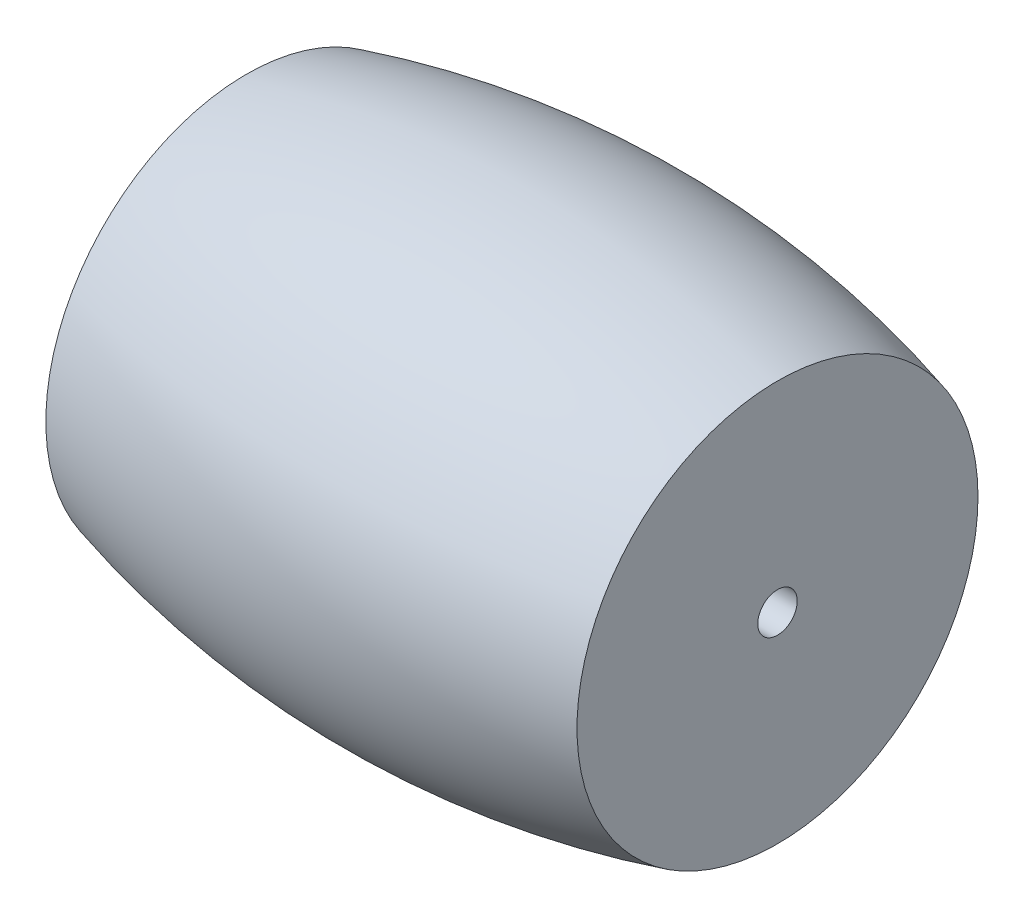
SolidWorks part; units mm, degrees
material "PET"
ref_plane "Front Plane" through (0, 0, 0) normal (0, 0, 1) x (1, 0, 0)
ref_plane "Top Plane" through (0, 0, 0) normal (0, 1, 0) x (1, 0, 0)
ref_plane "Right Plane" through (0, 0, 0) normal (1, 0, 0) x (0, 0, -1)
sketch "Sketch1" plane through (0, 0, 0) normal (0, 0, 1) x (1, 0, 0)
  line L6 (55.9339, -48.4402) -> (27.967, 0)
  line L7 (27.967, 0) -> (-27.967, 0)
  line L8 (-27.967, 0) -> (-55.9339, -48.4402)
  line L9 (-55.9339, -48.4402) -> (-27.967, -96.8804)
  line L10 (-27.967, -96.8804) -> (27.967, -96.8804)
  line L11 (27.967, -96.8804) -> (55.9339, -48.4402)
  line L13 (27.967, 0) -> (-27.967, 0)
  line L18 (-16.8232, 12.7) -> (-16.8232, 0) construction
  line L19 (-16.8232, 12.7) -> (-16.8232, 0)
  line L20 (16.8232, 12.7) -> (16.8232, 0) construction
  line L21 (16.8232, 12.7) -> (16.8232, 0)
  circle A0 centre (0, -48.4402) radius 63.4125 construction
  circle A1 centre (0, -48.4402) radius 63.4125
  dimension "D1" = 0
sketch "Sketch2" plane through (0, 0, 0) normal (0, 0, 1) x (1, 0, 0)
  line L0 (-16.8232, 12.7) -> (-16.8232, 0) construction
  line L1 (-16.8232, 12.7) -> (-16.8232, 1.25)
  line L2 (27.967, 0) -> (-27.967, 0) construction
  line L3 (27.967, 0) -> (-27.967, 0) construction
  line L4 (16.8232, 12.7) -> (16.8232, 0) construction
  line L5 (16.8232, 12.7) -> (16.8232, 1.25)
  line L6 (-16.8232, 1.25) -> (16.8232, 1.25)
  circle A0 centre (0, -48.4402) radius 63.4125 construction
  arc A1 (16.8232, 12.7) -> (-16.8232, 12.7) centre (0, -48.4402) ccw
  dimension "D1" = 1.25
revolve "Revolve1" add sketch "Sketch2" angle 360 about L3
